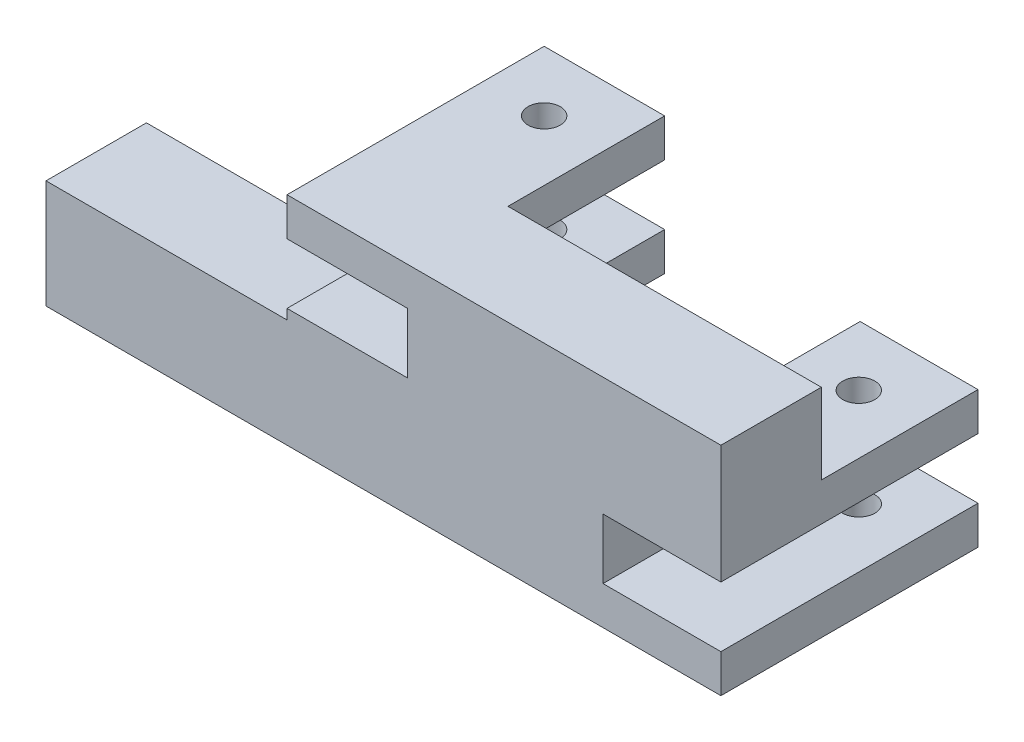
SolidWorks part; units mm, degrees
material "Ductile Iron"
ref_plane "Front Plane" through (0, 0, 0) normal (0, 0, 1) x (1, 0, 0)
ref_plane "Top Plane" through (0, 0, 0) normal (0, 1, 0) x (1, 0, 0)
ref_plane "Right Plane" through (0, 0, 0) normal (1, 0, 0) x (0, 0, -1)
sketch "Sketch1" plane through (0, 0, 0) normal (0, 0, 1) x (1, 0, 0)
  line L0 (-54, 27) -> (54, 27)
  line L5 (54, 27) -> (54, -2.5)
  line L6 (54, -2.5) -> (24.6547, -2.5)
  line L7 (24.6547, -2.5) -> (24.6547, -17.5)
  line L8 (24.6547, -17.5) -> (54, -17.5)
  line L9 (54, -17.5) -> (54, -27)
  line L10 (54, -27) -> (-54, -27)
  line L11 (-54, -27) -> (-54, 2.5)
  line L12 (-54, 2.5) -> (-24, 2.5)
  line L13 (-24, 2.5) -> (-24, 17.5)
  line L14 (-24, 17.5) -> (-54, 17.5)
  line L15 (-54, 17.5) -> (-54, 27)
  line L17 (-39, 17.5) -> (-39, 2.5) construction
  point P17 (0, 27)
  point P18 (0, -27)
  dimension "D5" = 15
  dimension "D1" = 30
  dimension "D2" = 39
  dimension "D6" = 15
  dimension "D3" = 5
  dimension "D4" = 2.5
  dimension "D7" = 9.5
  dimension "D8" = 9.5
extrude "Boss-Extrude1" add sketch "Sketch1" along normal blind 25
sketch "Sketch4" plane through (0, 0, 0) normal (0, 0, -1) x (-1, 0, 0)
  line L0 (-54, -2.5) -> (-54, 27) construction
  line L1 (-54, 7) -> (-24.6547, 7)
  line L2 (-54, 7) -> (-54, -2.5)
  line L3 (-54, -2.5) -> (-24.6547, -2.5)
  line L4 (-24.6547, 7) -> (-24.6547, -2.5)
  line L5 (-54, -17.5) -> (-24.6547, -17.5)
  line L6 (-54, -17.5) -> (-54, -27)
  line L7 (-54, -27) -> (-24.6547, -27)
  line L8 (-24.6547, -17.5) -> (-24.6547, -27)
  line L9 (-54, 27) -> (54, 27) construction
  line L10 (24, 2.5) -> (54, 2.5)
  line L11 (24, 2.5) -> (24, -7)
  line L12 (24, -7) -> (54, -7)
  line L13 (54, 2.5) -> (54, -7)
  line L14 (54, 17.5) -> (24, 17.5)
  line L15 (54, 17.5) -> (54, 27)
  line L16 (54, 27) -> (24, 27)
  line L17 (24, 17.5) -> (24, 27)
  line L19 (54, -27) -> (-54, -27) construction
extrude "Boss-Extrude2" add sketch "Sketch4" along normal blind 39
sketch "Sketch2" plane through (0, 27, 0) normal (0, 1, 0) x (1, 0, 0)
  line L0 (-39, 24) -> (39.3273, 24) construction
  line L1 (-39, 24) -> (-39, 39) construction
  line L2 (24.6547, 39) -> (54, 39) construction
  line L3 (-54, 39) -> (-24, 39) construction
  line L4 (39.3273, 24) -> (39.3273, 39) construction
  circle A1 centre (39.3273, 24) radius 4
  circle A2 centre (-39, 24) radius 4
  dimension "D3" = 8
  dimension "D1" = 15
extrude "Actuator Shaft Passthrough" cut sketch "Sketch2" against normal offset from surface (54.5 mm away) 10 up to face at (36.3928, -17.5, -5.6) offset beyond the face yes
sketch "Sketch6" plane through (54, 0, 0) normal (1, 0, 0) x (0, 0, -1)
  line L1 (-25, 27) -> (0, 27)
  line L2 (-25, 27) -> (-25, 0)
  line L3 (-25, 0) -> (0, 0)
  line L4 (0, 27) -> (0, 0)
  line L5 (-25, 27) -> (0, 0) construction
  line L6 (-25, 0) -> (0, 27) construction
  point P4 (-12.5, 13.5)
extrude "Boss-Extrude3" [suppressed] add sketch "Sketch6" along normal blind 60 contours L4 L3 L2 L1
sketch "Sketch7" plane through (-54, 0, 0) normal (-1, 0, 0) x (0, 0, 1)
  line L1 (25, -27) -> (0, -27)
  line L2 (25, -27) -> (25, 0)
  line L3 (25, 0) -> (0, 0)
  line L4 (0, -27) -> (0, 0)
  line L5 (25, -27) -> (0, 0) construction
  line L6 (25, 0) -> (0, -27) construction
  point P4 (12.5, -13.5)
extrude "Boss-Extrude4" add sketch "Sketch7" along normal blind 60
sketch "Sketch8" [suppressed] plane through (0, 0, 0) normal (0, 1, 0) x (1, 0, 0)
  line L0 (-114, -12.5) -> (99, -12.5) construction
  line L1 (-114, -25) -> (-114, 0) construction
  line L2 (114, -25) -> (114, 0) construction
  circle A0 centre (-99, -12.5) radius 4.4
  circle A1 centre (99, -12.5) radius 4.4
  dimension "D1" = 8.8
  dimension "D2" = 15
  dimension "D3" = 15
extrude "Cut-Extrude1" [suppressed] cut sketch "Sketch8" against normal through all both and the other way through all
sketch "Sketch9" [suppressed] plane through (0, 27, 0) normal (0, 1, 0) x (1, 0, 0)
  line L1 (91, -20.5) -> (107, -20.5) construction
  line L2 (91, -20.5) -> (91, -4.5) construction
  line L3 (91, -4.5) -> (107, -4.5) construction
  line L4 (107, -20.5) -> (107, -4.5) construction
  line L5 (91, -20.5) -> (107, -4.5) construction
  line L6 (91, -4.5) -> (107, -20.5) construction
  circle A0 centre (107, -4.5) radius 2.05
  circle A1 centre (91, -4.5) radius 2.05
  circle A2 centre (91, -20.5) radius 2.05
  circle A3 centre (107, -20.5) radius 2.05
  point P0 (99, -12.5)
  dimension "D3" = 4.1
  dimension "D1" = 16
  dimension "D2" = 16
extrude "Cut-Extrude2" [suppressed] cut sketch "Sketch9" against normal blind 10
equation "\"D4@Sketch1\"=\"D3@Sketch1\"/2"
